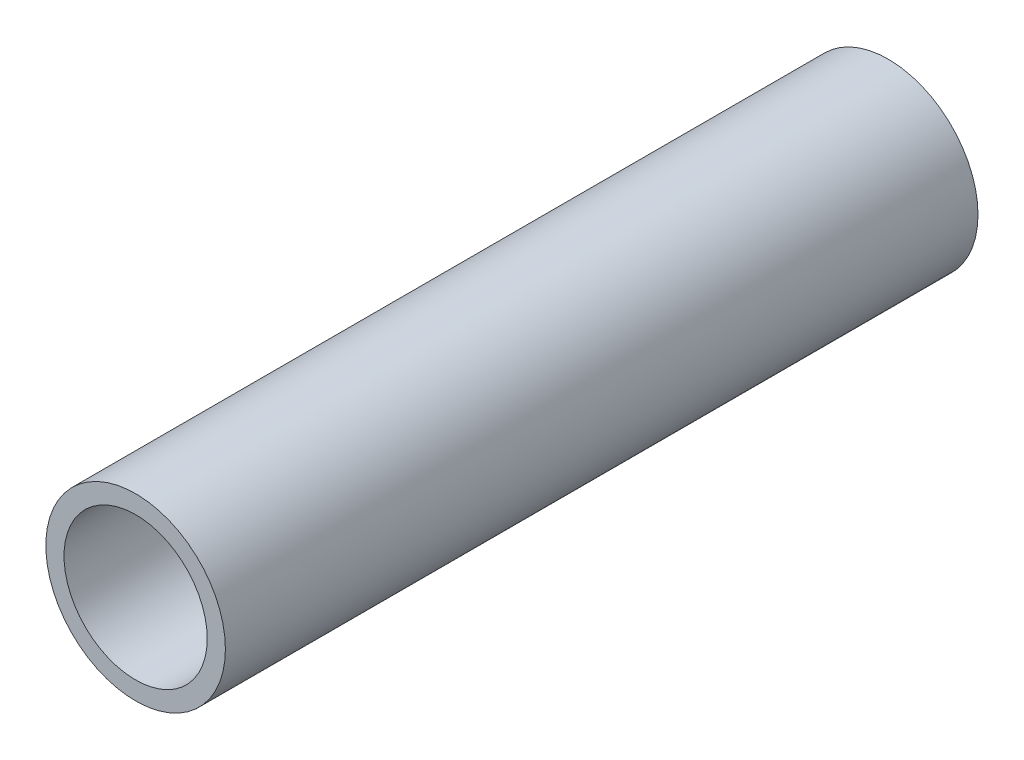
SolidWorks part; units mm, degrees
ref_plane "Front Plane" through (0, 0, 0) normal (0, 0, 1) x (1, 0, 0)
ref_plane "Top Plane" through (0, 0, 0) normal (0, 1, 0) x (1, 0, 0)
ref_plane "Right Plane" through (0, 0, 0) normal (1, 0, 0) x (0, 0, -1)
sketch "Sketch1" plane through (0, 0, 0) normal (0, 0, 1) x (1, 0, 0)
  circle A0 centre (0, 0) radius 16.7005
  dimension "Pipe OD" = 33.401
extrude "Extrude-Thin1" add sketch "Sketch1" along normal mid plane 140 thin thin type one direction reverse wall 3.3782
